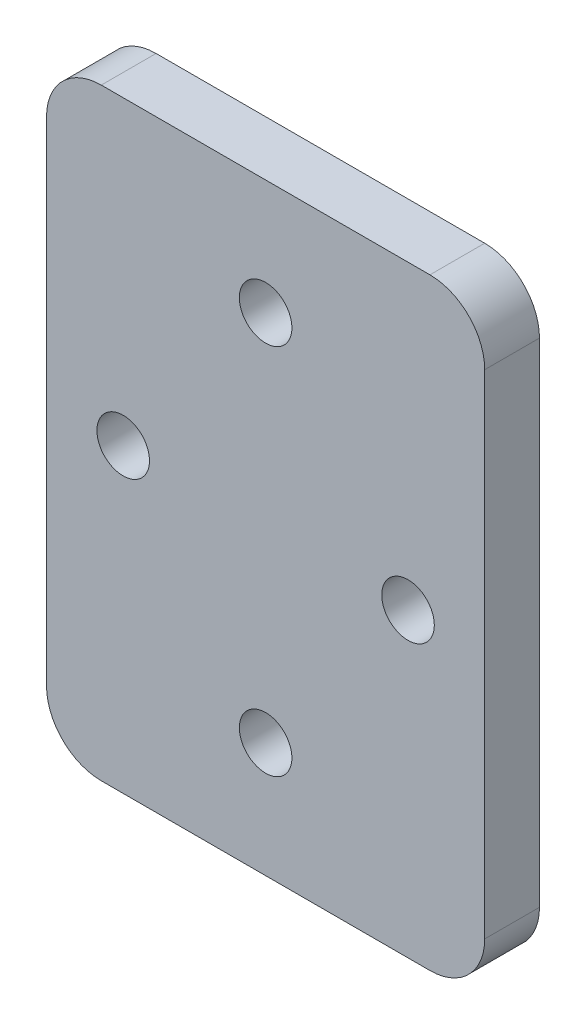
SolidWorks part; units mm, degrees
ref_plane "Front Plane" through (0, 0, 0) normal (0, 0, 1) x (1, 0, 0)
ref_plane "Top Plane" through (0, 0, 0) normal (0, 1, 0) x (1, 0, 0)
ref_plane "Right Plane" through (0, 0, 0) normal (1, 0, 0) x (0, 0, -1)
sketch "Sketch1" plane through (0, 0, 0) normal (0, 0, 1) x (1, 0, 0)
  line L1 (-20, 27.5) -> (20, 27.5)
  line L2 (-20, 27.5) -> (-20, -27.5)
  line L3 (-20, -27.5) -> (20, -27.5)
  line L4 (20, 27.5) -> (20, -27.5)
  line L5 (0, -27.5) -> (0, 27.5) construction
  line L6 (-20, 0) -> (20, 0) construction
  circle A0 centre (0, 17) radius 2.4
  circle A1 centre (13, 0) radius 2.4
  circle A2 centre (0, -17) radius 2.4
  circle A3 centre (-13, 0) radius 2.4
  point P0 (0, 0)
  dimension "D3" = 4.8
  dimension "D5" = 4.8
  dimension "D1" = 55
  dimension "D2" = 40
  dimension "D4" = 17
  dimension "D6" = 13
extrude "Boss-Extrude1" add sketch "Sketch1" along normal blind 5
fillet "Fillet1" radius 5 4 edges at (-20, 27.5, 2.5) (-20, -27.5, 2.5) (20, -27.5, 2.5) (20, 27.5, 2.5)
